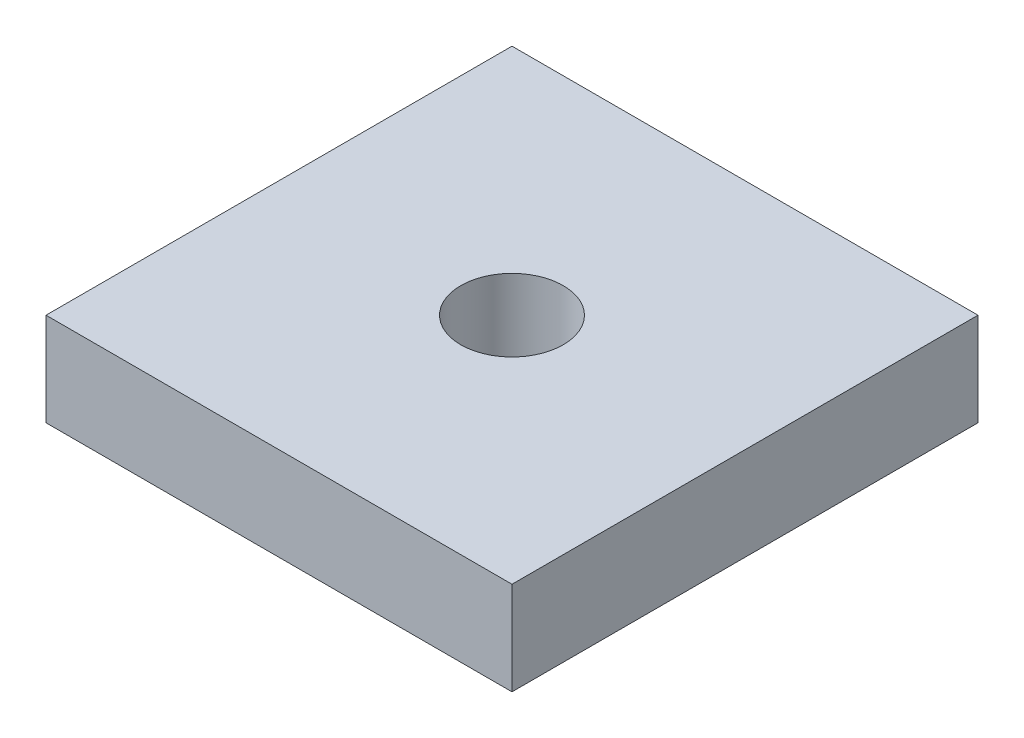
SolidWorks part; units mm, degrees
ref_plane "前视基准面" through (0, 0, 0) normal (0, 0, 1) x (1, 0, 0)
ref_plane "上视基准面" through (0, 0, 0) normal (0, 1, 0) x (1, 0, 0)
ref_plane "右视基准面" through (0, 0, 0) normal (1, 0, 0) x (0, 0, -1)
sketch "草图1" plane through (0, 0, 0) normal (-1, 0, 0) x (0, 0, 1)
  line L0 (-2165.8052, -788.1153) -> (-2180.8052, -788.1153)
  line L1 (-2180.8052, -788.1153) -> (-2180.8052, -785.1153)
  line L2 (-2180.8052, -785.1153) -> (-2165.8052, -785.1153)
  line L3 (-2165.8052, -785.1153) -> (-2165.8052, -788.1153)
extrude "凸台-拉伸1" add sketch "草图1" along normal blind 15
hole_wizard "M4 螺纹孔1" positions "草图3" profile "草图2" tap size "M4" standard "GB"
sketch "草图3" plane through (0, -785.1153, 0) normal (0, 1, 0) x (-1, 0, 0)
  line L0 (15, -2165.8052) -> (0, -2165.8052) construction
  line L1 (15, -2165.8052) -> (15, -2180.8052) construction
  point P0 (7.5, -2173.3052)
  dimension "D1" = 7.5
  dimension "D2" = 7.5
sketch "草图2" plane through (-7.5, -785.1153, -2173.3052) normal (1, 0, 0) x (0, 0, 1)
  line L0 (0, 0) -> (0, 12.4914)
  line L1 (0, 12.4914) -> (1.65, 11.5)
  line L2 (1.65, 11.5) -> (1.65, 0)
  line L5 (1.65, 0) -> (0, 0)
  line L10 (0, 12.4914) -> (-1.65, 11.5) construction
  line L11 (0, -6.35) -> (0, 107.95) construction
  dimension "螺纹孔钻头直径" = 3.3
  dimension "螺纹孔钻头深度" = 11.5
  dimension "导头角度" = 118
cosmetic thread "孔螺蚊线1" parameters "D1"=3, "D2"=4
